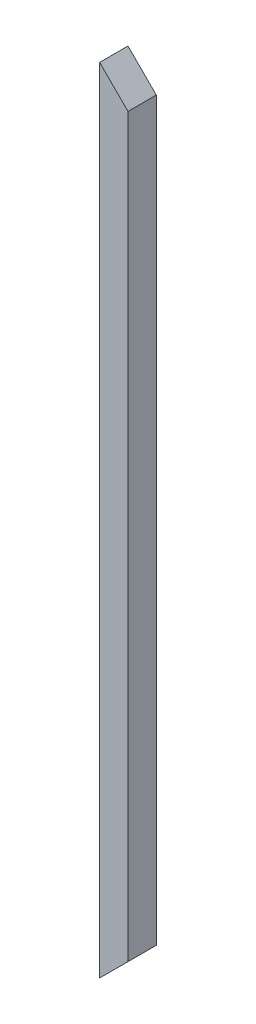
SolidWorks part; units mm, degrees
ref_plane "Front Plane" through (0, 0, 0) normal (0, 0, 1) x (1, 0, 0)
ref_plane "Top Plane" through (0, 0, 0) normal (0, 1, 0) x (1, 0, 0)
ref_plane "Right Plane" through (0, 0, 0) normal (1, 0, 0) x (0, 0, -1)
sketch "Sketch1" plane through (0, 0, 0) normal (0, 1, 0) x (1, 0, 0)
  line L1 (7.5, 7.5) -> (-7.5, 7.5)
  line L2 (7.5, 7.5) -> (7.5, -7.5)
  line L3 (7.5, -7.5) -> (-7.5, -7.5)
  line L4 (-7.5, 7.5) -> (-7.5, -7.5)
  line L5 (7.5, 7.5) -> (-7.5, -7.5) construction
  line L6 (7.5, -7.5) -> (-7.5, 7.5) construction
  point P0 (0, 0)
  dimension "D1" = 15
  dimension "D2" = 15
extrude "Boss-Extrude1" add sketch "Sketch1" along normal blind 420
sketch "Sketch2" plane through (0, 0, 7.5) normal (0, 0, 1) x (1, 0, 0)
  line L0 (-7.5, 420) -> (7.5, 405)
  line L1 (7.5, 420) -> (7.5, 0) construction
  line L2 (7.5, 405) -> (7.5, 420)
  line L3 (7.5, 420) -> (-7.5, 420)
  line L4 (-7.5, 0) -> (7.5, 15)
  line L5 (7.5, 15) -> (7.5, 0)
  line L6 (7.5, 0) -> (-7.5, 0)
  dimension "D1" = 45
  dimension "D2" = 45
extrude "Cut-Extrude1" cut sketch "Sketch2" against normal blind 30
